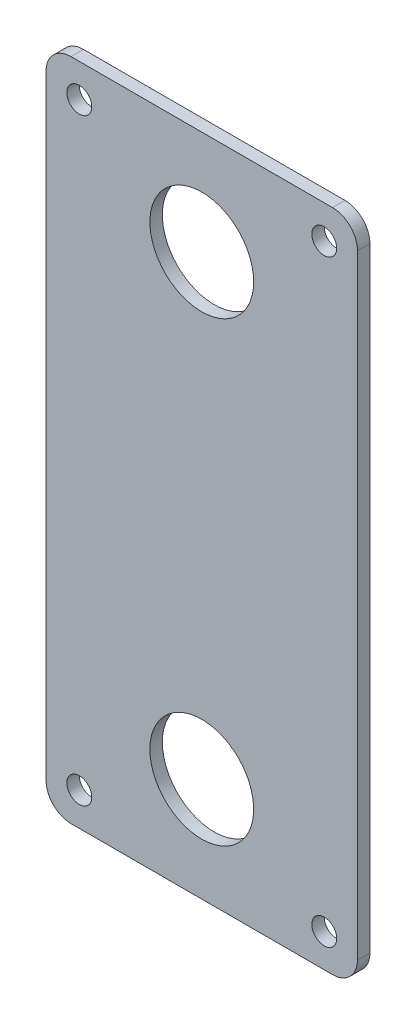
SolidWorks part; units mm, degrees
ref_plane "Alzado" through (0, 0, 0) normal (0, 0, 1) x (1, 0, 0)
ref_plane "Planta" through (0, 0, 0) normal (0, 1, 0) x (1, 0, 0)
ref_plane "Vista lateral" through (0, 0, 0) normal (1, 0, 0) x (0, 0, -1)
sketch "Croquis1" plane through (0, 0, 0) normal (0, 0, 1) x (1, 0, 0)
  line L0 (0, -80) -> (0, 80) construction
  line L1 (37.5, 80) -> (-37.5, 80)
  line L2 (37.5, 80) -> (37.5, -80)
  line L3 (37.5, -80) -> (-37.5, -80)
  line L4 (-37.5, 80) -> (-37.5, -80)
  line L5 (37.5, 80) -> (-37.5, -80) construction
  line L6 (37.5, -80) -> (-37.5, 80) construction
  line L7 (-37.5, 0) -> (37.5, 0) construction
  circle A0 centre (0, 55) radius 12.5
  circle A1 centre (0, -55) radius 12.5
  circle A2 centre (-29.5, 72) radius 3
  circle A3 centre (29.5, 72) radius 3
  circle A4 centre (-29.5, -72) radius 3
  circle A5 centre (29.5, -72) radius 3
  point P0 (0, 0)
  dimension "D3" = 25
  dimension "D5" = 6
  dimension "D1" = 75
  dimension "D2" = 160
  dimension "D4" = 55
  dimension "D6" = 8
  dimension "D7" = 8
extrude "Saliente-Extruir1" add sketch "Croquis1" along normal blind 3
fillet "Redondeo1" radius 6 4 edges at (-37.5, 80, 1.5) (37.5, 80, 1.5) (37.5, -80, 1.5) (-37.5, -80, 1.5)
